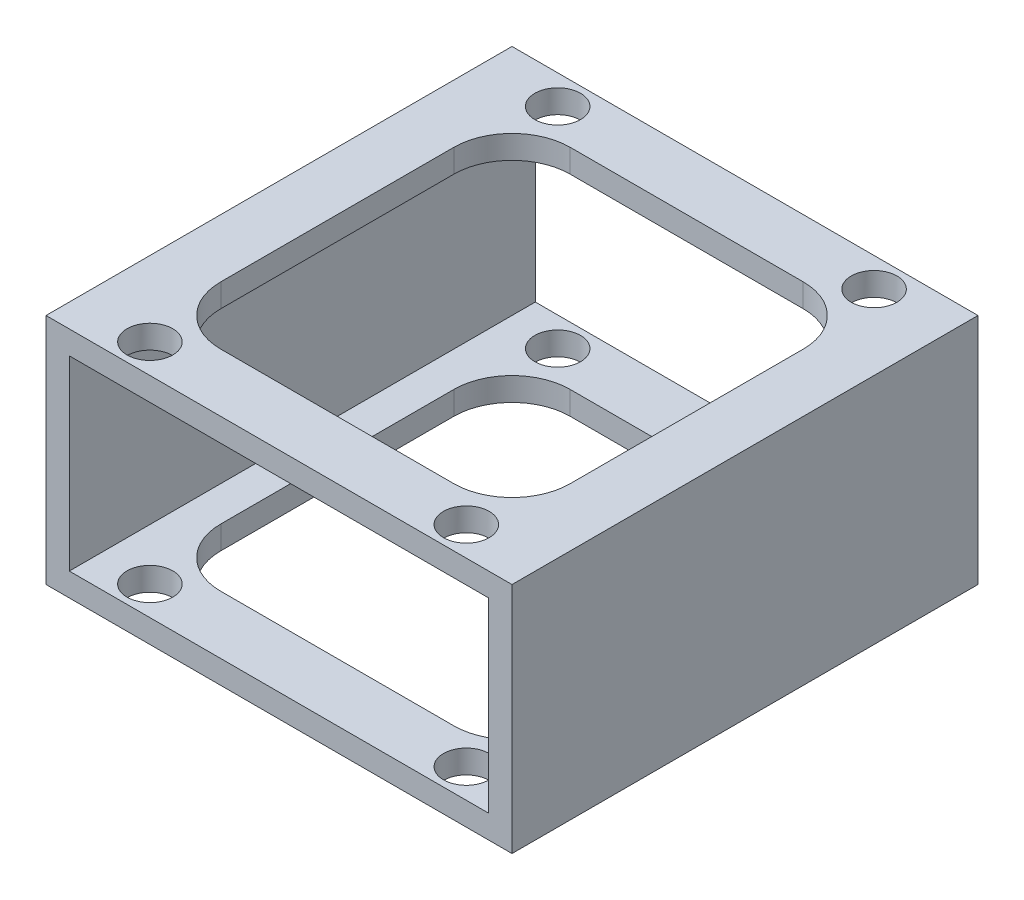
SolidWorks part; units mm, degrees
ref_plane "Front" through (0, 0, 0) normal (0, 0, 1) x (1, 0, 0)
ref_plane "Top" through (0, 0, 0) normal (0, 1, 0) x (1, 0, 0)
ref_plane "Right" through (0, 0, 0) normal (1, 0, 0) x (0, 0, -1)
sketch "Sketch1" plane through (0, 0, 0) normal (0, 0, 1) x (1, 0, 0)
  line L1 (-25.4, -12.7) -> (25.4, -12.7)
  line L2 (-25.4, -12.7) -> (-25.4, 12.7)
  line L3 (-25.4, 12.7) -> (25.4, 12.7)
  line L4 (25.4, -12.7) -> (25.4, 12.7)
  line L5 (-25.4, -12.7) -> (25.4, 12.7) construction
  line L6 (-25.4, 12.7) -> (25.4, -12.7) construction
  point P0 (0, 0)
  dimension "D1" = 25.4
  dimension "D2" = 50.8
extrude "Extrude-Thin1" add sketch "Sketch1" along normal blind 50.8 thin thin type one direction reverse wall 2.54
sketch "Sketch2" plane through (0, 12.7, 0) normal (0, 1, 0) x (1, 0, 0)
  line L0 (-25.4, 0) -> (25.4, -50.8) construction
  line L1 (19.05, -44.45) -> (19.05, -6.35)
  line L2 (-12.7, -38.1) -> (12.7, -38.1) construction
  line L3 (-12.7, -38.1) -> (-12.7, -12.7) construction
  line L4 (-12.7, -12.7) -> (12.7, -12.7) construction
  line L5 (12.7, -38.1) -> (12.7, -12.7) construction
  line L6 (-12.7, -38.1) -> (12.7, -12.7) construction
  line L7 (-12.7, -12.7) -> (12.7, -38.1) construction
  line L8 (-19.05, -6.35) -> (19.05, -6.35)
  line L9 (-19.05, -44.45) -> (-19.05, -6.35)
  line L10 (-19.05, -44.45) -> (19.05, -44.45)
  arc A0 (-19.05, -12.7) -> (-12.7, -6.35) centre (-12.7, -12.7) cw
  arc A1 (12.7, -6.35) -> (19.05, -12.7) centre (12.7, -12.7) cw
  arc A2 (19.05, -38.1) -> (12.7, -44.45) centre (12.7, -38.1) cw
  arc A3 (-12.7, -44.45) -> (-19.05, -38.1) centre (-12.7, -38.1) cw
  point P4 (0, -25.4)
  point P28 (0, -25.4)
  dimension "D4" = 6.35
  dimension "D1" = 25.4
  dimension "D2" = 25.4
  dimension "D3" = 6.35
  dimension "D5" = 4
extrude "Cut-Extrude1" cut sketch "Sketch2" against normal through all contours A3 L10 A2 L1 A1 L8 A0 L9
sketch "Sketch3" plane through (0, 12.7, 0) normal (0, 1, 0) x (1, 0, 0)
  circle A8 centre (-17.2466, -47.625) radius 2.4892 construction
  circle A9 centre (17.2466, -47.625) radius 2.4892 construction
  circle A10 centre (17.2466, -3.175) radius 2.4892 construction
  circle A11 centre (-17.2466, -3.175) radius 2.4892 construction
  circle A12 centre (-17.2466, -47.625) radius 2.4892
  circle A13 centre (17.2466, -47.625) radius 2.4892
  circle A14 centre (17.2466, -3.175) radius 2.4892
  circle A15 centre (-17.2466, -3.175) radius 2.4892
extrude "Cut-Extrude2" cut sketch "Sketch3" against normal through all
